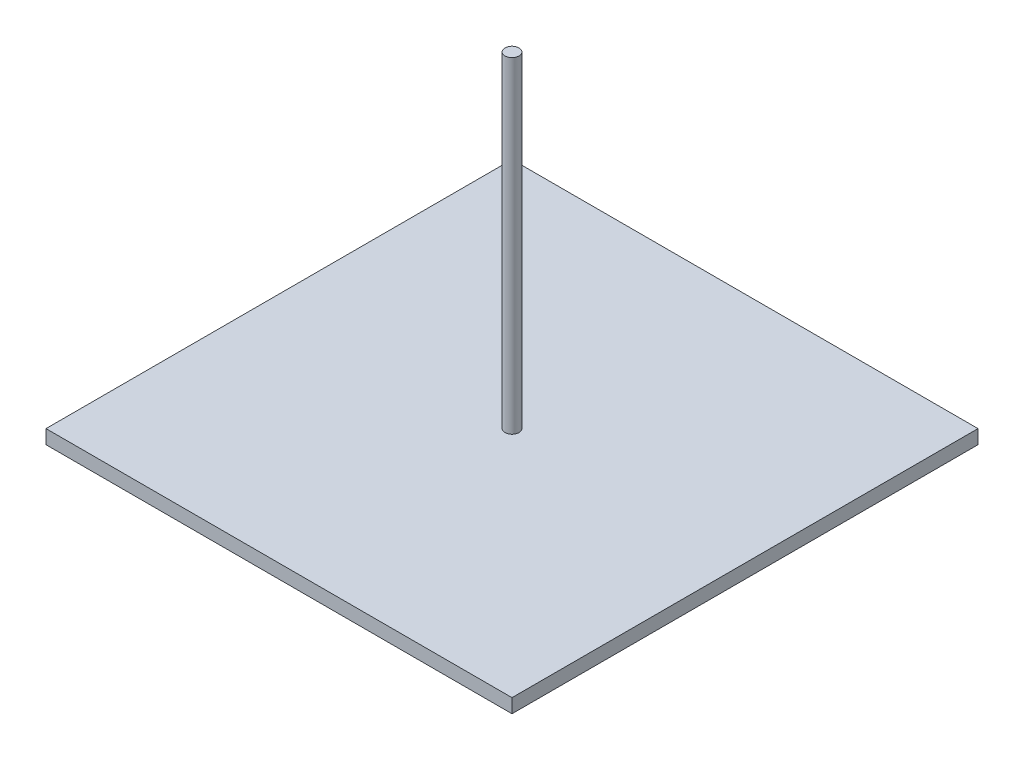
SolidWorks part; units mm, degrees
ref_plane "Piano frontale" through (0, 0, 0) normal (0, 0, 1) x (1, 0, 0)
ref_plane "Piano superiore" through (0, 0, 0) normal (0, 1, 0) x (1, 0, 0)
ref_plane "Piano destro" through (0, 0, 0) normal (1, 0, 0) x (0, 0, -1)
sketch "Schizzo1" plane through (0, -24.14, 0) normal (0, -1, 0) x (1, 0, 0)
  line L0 (-228.0625, -20.8002) -> (-228.0625, -54.6163) construction
  line L7 (-117.0625, -87.7082) -> (-217.0625, -87.7082)
  line L8 (-117.0625, -87.7082) -> (-117.0625, 12.2918)
  line L9 (-117.0625, 12.2918) -> (-217.0625, 12.2918)
  line L10 (-217.0625, -87.7082) -> (-217.0625, 12.2918)
  line L11 (-117.0625, -87.7082) -> (-217.0625, 12.2918) construction
  line L12 (-117.0625, 12.2918) -> (-217.0625, -87.7082) construction
  line L13 (-171.0625, -46.2735) -> (-171.0625, -29.143) construction
  point P0 (-132.0625, -37.7082)
  point P6 (-167.0625, -37.7082)
  point P13 (-228.0625, -37.7082)
  dimension "D3" = 100
  dimension "D4" = 0
  dimension "D5" = 4
extrude "Estrusione-Estrusione1" add sketch "Schizzo1" along normal blind 3 from offset 70
sketch "Schizzo2" plane through (0, -94.14, 0) normal (0, 1, 0) x (1, 0, 0)
  line L0 (-217.0625, -12.2918) -> (-117.0625, 87.7082) construction
  line L1 (-217.0625, 87.7082) -> (-117.0625, -12.2918) construction
  circle A0 centre (-167.0625, 37.7082) radius 1.5
extrude "Estrusione-Estrusione2" add sketch "Schizzo2" along normal up to surface (70 mm away)
